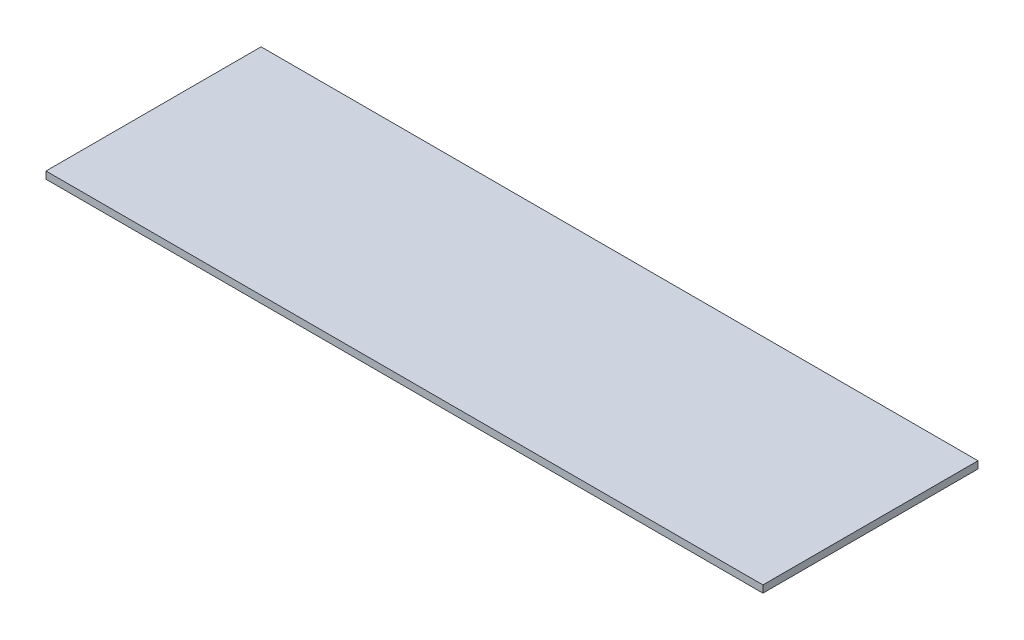
SolidWorks part; units mm, degrees
material "6061 Alloy"
ref_plane "Front Plane" through (0, 0, 0) normal (0, 0, 1) x (1, 0, 0)
ref_plane "Top Plane" through (0, 0, 0) normal (0, 1, 0) x (1, 0, 0)
ref_plane "Right Plane" through (0, 0, 0) normal (1, 0, 0) x (0, 0, -1)
sketch "Sketch1" plane through (0, 0, 0) normal (0, 1, 0) x (1, 0, 0)
  line L1 (0, 0) -> (-1000, 0)
  line L2 (0, 0) -> (0, 300)
  line L3 (0, 300) -> (-1000, 300)
  line L4 (-1000, 0) -> (-1000, 300)
  dimension "D1" = 300
  dimension "D2" = 1000
extrude "Extrude1" add sketch "Sketch1" along normal blind 10
